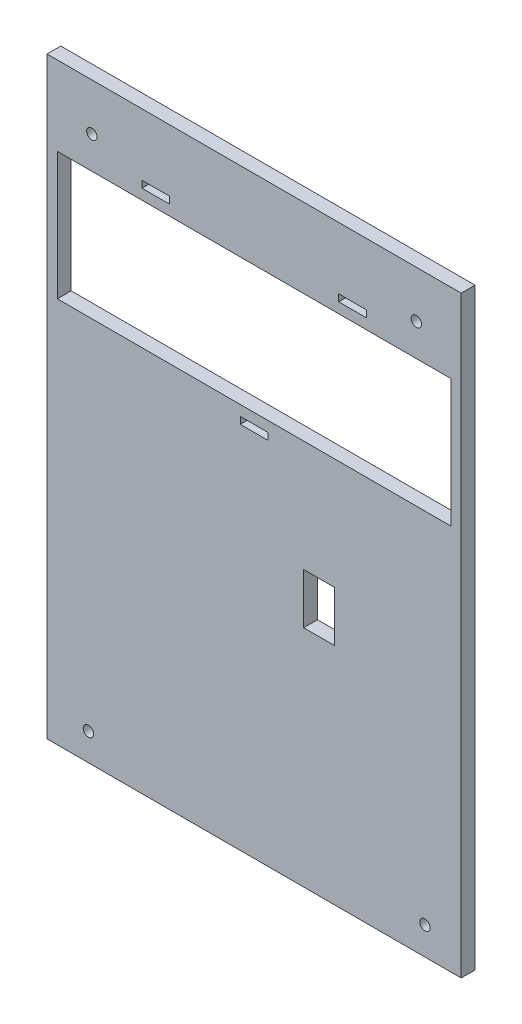
SolidWorks part; units mm, degrees
ref_plane "Front Plane" through (0, 0, 0) normal (0, 0, 1) x (1, 0, 0)
ref_plane "Top Plane" through (0, 0, 0) normal (0, 1, 0) x (1, 0, 0)
ref_plane "Right Plane" through (0, 0, 0) normal (1, 0, 0) x (0, 0, -1)
sketch "Sketch1" plane through (0, 0, 0) normal (0, 0, 1) x (1, 0, 0)
  line L0 (0, 163.8989) -> (120, 163.8989)
  line L1 (120, 163.8989) -> (120, -7.9289)
  line L2 (120, -7.9289) -> (0, -7.9289)
  line L3 (0, -7.9289) -> (0, 163.8989)
  line L4 (3, 140.97) -> (117, 140.97)
  line L5 (117, 140.97) -> (117, 103.97)
  line L7 (3, 140.97) -> (3, 103.97)
  line L9 (3, 103.97) -> (117, 103.97)
  line L10 (60, 140.97) -> (60, 103.97) construction
  line L11 (3, 122.47) -> (60, 122.47) construction
  line L12 (31.5, 140.97) -> (31.5, 143.97) construction
  line L13 (31.5, 143.97) -> (27.5, 143.97)
  line L14 (27.5, 143.97) -> (27.5, 145.97)
  line L15 (27.5, 145.97) -> (35.5, 145.97)
  line L16 (88.5, 140.97) -> (88.5, 143.97) construction
  line L17 (35.5, 145.97) -> (35.5, 143.97)
  line L18 (35.5, 143.97) -> (31.5, 143.97)
  line L19 (92.5, 145.97) -> (84.5, 145.97)
  line L20 (84.5, 145.97) -> (84.5, 143.97)
  line L21 (92.5, 143.97) -> (92.5, 145.97)
  line L22 (88.5, 143.97) -> (92.5, 143.97)
  line L23 (84.5, 143.97) -> (88.5, 143.97)
  line L24 (60, 103.97) -> (60, 98.97) construction
  line L25 (60, 98.97) -> (56, 98.97)
  line L26 (56, 98.97) -> (56, 100.97)
  line L27 (56, 100.97) -> (64, 100.97)
  line L28 (64, 100.97) -> (64, 98.97)
  line L29 (64, 98.97) -> (60, 98.97)
  circle A0 centre (13, 150.3131) radius 1.5
  circle A1 centre (107, 150.3131) radius 1.5
  circle A2 centre (109.5, 0.1569) radius 1.5
  circle A3 centre (12, 0) radius 1.5
  dimension "D5" = 3
  dimension "D1" = 37
  dimension "D2" = 114
  dimension "D3" = 171.8279
  dimension "D4" = 120
extrude "Boss-Extrude1" add sketch "Sketch1" along normal blind 4 contours L7 L9 L5 L4 | A0 | A1 | A2 | A3 | L18 L17 L15 L14 L13 | L20 L23 L22 L21 L19 | L0 L1 L2 L3 | L27 L28 L29 L25 L26
sketch "Sketch2" plane through (0, 0, 0) normal (0, 0, -1) x (-1, 0, 0)
  line L1 (-74.3566, 57.1261) -> (-83.3566, 57.1261)
  line L2 (-74.3566, 57.1261) -> (-74.3566, 71.7261)
  line L3 (-74.3566, 71.7261) -> (-83.3566, 71.7261)
  line L4 (-83.3566, 57.1261) -> (-83.3566, 71.7261)
  line L5 (-74.3566, 57.1261) -> (-83.3566, 71.7261) construction
  line L6 (-74.3566, 71.7261) -> (-83.3566, 57.1261) construction
  point P0 (-78.8566, 64.4261)
  dimension "D1" = 14.6
  dimension "D2" = 9
extrude "Cut-Extrude1" cut sketch "Sketch2" against normal through all
